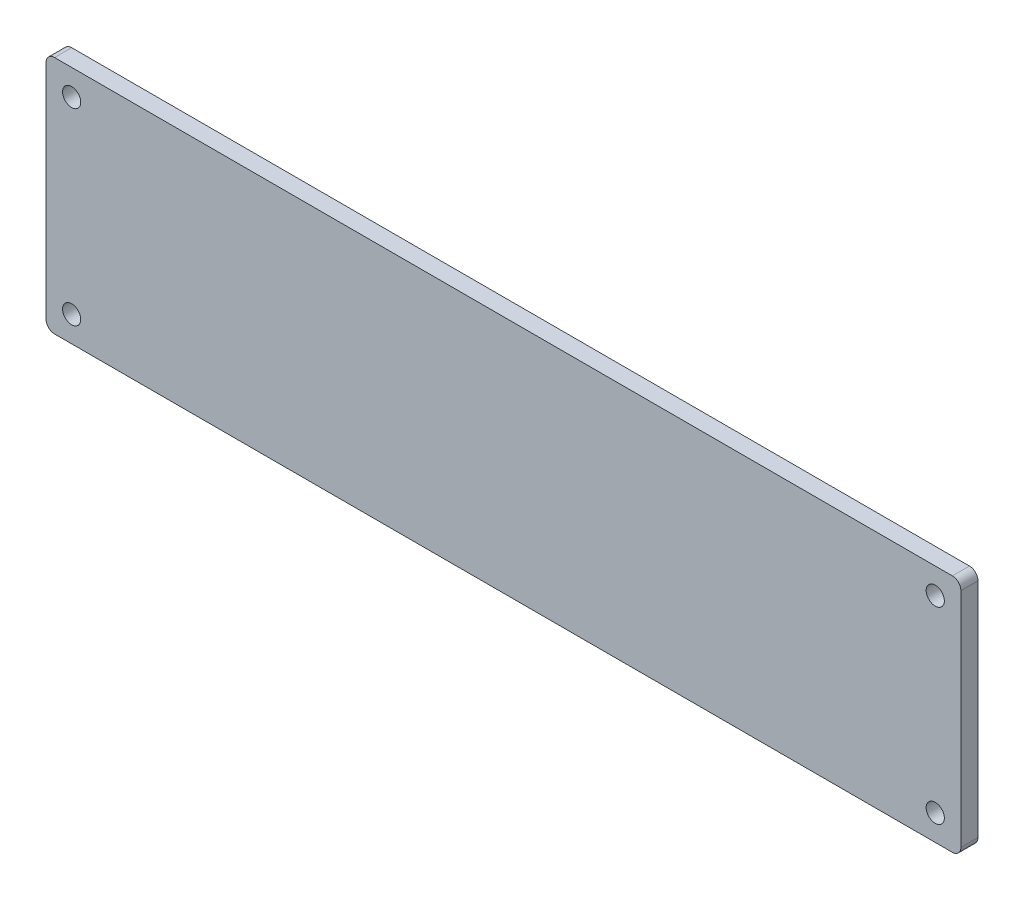
SolidWorks part; units mm, degrees
material "PC High Viscosity"
ref_plane "Front Plane" through (0, 0, 0) normal (0, 0, 1) x (1, 0, 0)
ref_plane "Top Plane" through (0, 0, 0) normal (0, 1, 0) x (1, 0, 0)
ref_plane "Right Plane" through (0, 0, 0) normal (1, 0, 0) x (0, 0, -1)
ref_plane "Plane1" through (0, 0, 0) normal (0, 0, -1) x (-1, 0, 0)
sketch "Sketch1" plane through (0, 0, 0) normal (0, 0, -1) x (-1, 0, 0)
  line L0 (-169.8625, -44.45) -> (169.8625, -44.45)
  line L1 (169.8625, -44.45) -> (169.8625, 44.45)
  line L2 (169.8625, 44.45) -> (-169.8625, 44.45)
  line L3 (-169.8625, 44.45) -> (-169.8625, -44.45)
  point P0 (0, 44.45)
  point P30 (169.8625, 0)
  dimension "D1" = 88.9
  dimension "D2" = 339.725
extrude "Boss-Extrude1" add sketch "Sketch1" against normal blind 6.35
hole_wizard "1/4 Clearance Hole1" positions "Sketch2" profile "Sketch3" hole size "1/4" standard "ANSI Inch" end condition through all
sketch "Sketch2" plane through (0, 0, 6.35) normal (0, 0, 1) x (1, 0, 0)
  line L1 (-160.3375, 34.925) -> (160.3375, 34.925) construction
  line L2 (-160.3375, 34.925) -> (-160.3375, -34.925) construction
  line L3 (-160.3375, -34.925) -> (160.3375, -34.925) construction
  line L4 (160.3375, 34.925) -> (160.3375, -34.925) construction
  line L5 (-169.8625, 44.45) -> (169.8625, 44.45) construction
  line L6 (-169.8625, -44.45) -> (-169.8625, 44.45) construction
  line L7 (169.8625, -44.45) -> (-169.8625, -44.45) construction
  line L8 (-160.3375, 0) -> (160.3375, 0) construction
  point P0 (-160.3375, 34.925)
  point P2 (-160.3375, -34.925)
  point P4 (160.3375, 34.925)
  point P6 (160.3375, -34.925)
  point P54 (-160.3375, 0)
  point P55 (-169.8625, 0)
  point P56 (0, -34.925)
  point P59 (0, -44.45)
  dimension "D1" = 9.525
  dimension "D2" = 9.525
sketch "Sketch3" plane through (-160.3375, 34.925, 6.35) normal (1, 0, 0) x (0, -1, 0)
  line L0 (0, 0) -> (0, 6.35)
  line L1 (0, 6.35) -> (3.3782, 6.35)
  line L2 (3.3782, 6.35) -> (3.3782, 0)
  line L5 (3.3782, 0) -> (0, 0)
  line L11 (0, -6.35) -> (0, 107.95) construction
  dimension "Thru Hole Dia." = 6.7564
  dimension "Thru Hole Depth" = 6.35
fillet "Fillet1" radius 3.175 4 edges at (169.8625, 44.45, 3.175) (169.8625, -44.45, 3.175) (-169.8625, 44.45, 3.175) (-169.8625, -44.45, 3.175)
